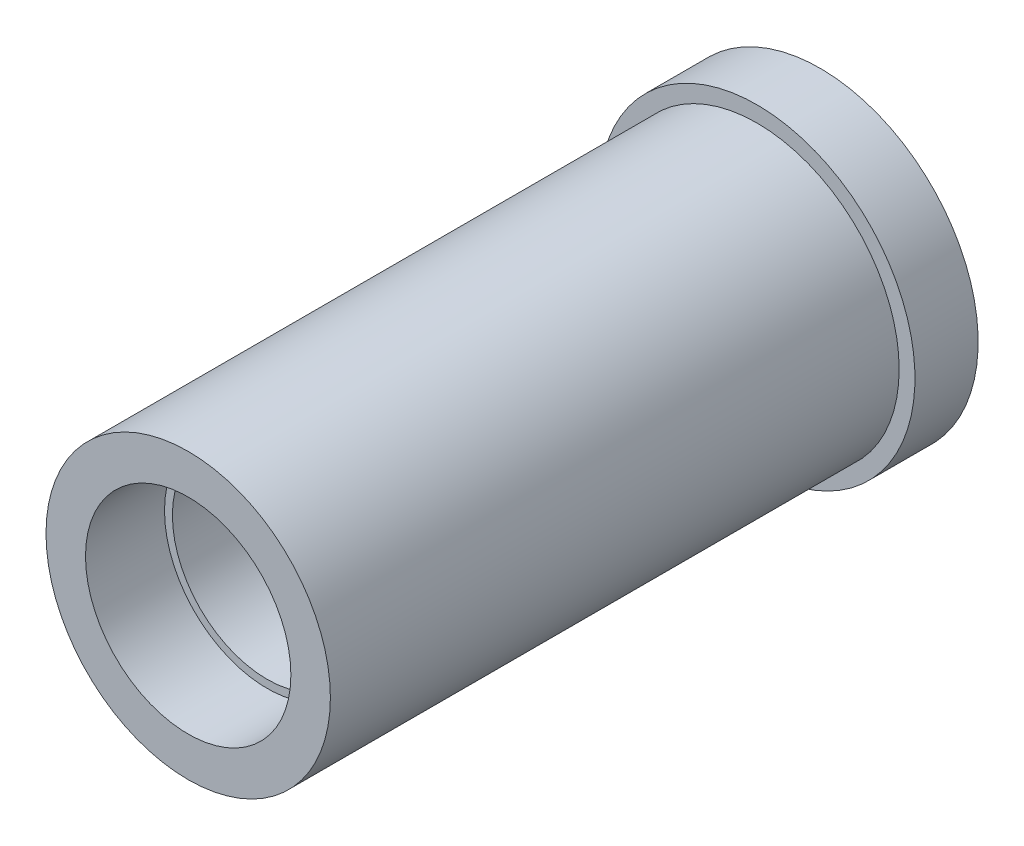
SolidWorks part; units mm, degrees
ref_plane "前视基准面" through (0, 0, 0) normal (0, 0, 1) x (1, 0, 0)
ref_plane "上视基准面" through (0, 0, 0) normal (0, 1, 0) x (1, 0, 0)
ref_plane "右视基准面" through (0, 0, 0) normal (1, 0, 0) x (0, 0, -1)
sketch "草图1" plane through (0, 0, 0) normal (0, 0, 1) x (1, 0, 0)
  circle A0 centre (0, 0) radius 9
  circle A1 centre (0, 0) radius 6
  dimension "D1" = 18
  dimension "D2" = 12
extrude "凸台-拉伸1" add sketch "草图1" along normal blind 40
sketch "草图2" plane through (0, 0, 40) normal (0, 0, 1) x (1, 0, 0)
  circle A0 centre (0, 0) radius 6.5
  dimension "D1" = 13
extrude "切除-拉伸1" cut sketch "草图2" against normal blind 5
sketch "草图3" plane through (0, 0, 0) normal (0, 0, -1) x (-1, 0, 0)
  circle A0 centre (0, 0) radius 6.5
  dimension "D1" = 13
extrude "切除-拉伸2" cut sketch "草图3" against normal blind 5
sketch "草图4" plane through (0, 0, 0) normal (0, 0, -1) x (-1, 0, 0)
  circle A0 centre (0, 0) radius 10
  circle A1 centre (0, 0) radius 9
  dimension "D1" = 20
extrude "凸台-拉伸2" add sketch "草图4" against normal blind 4
